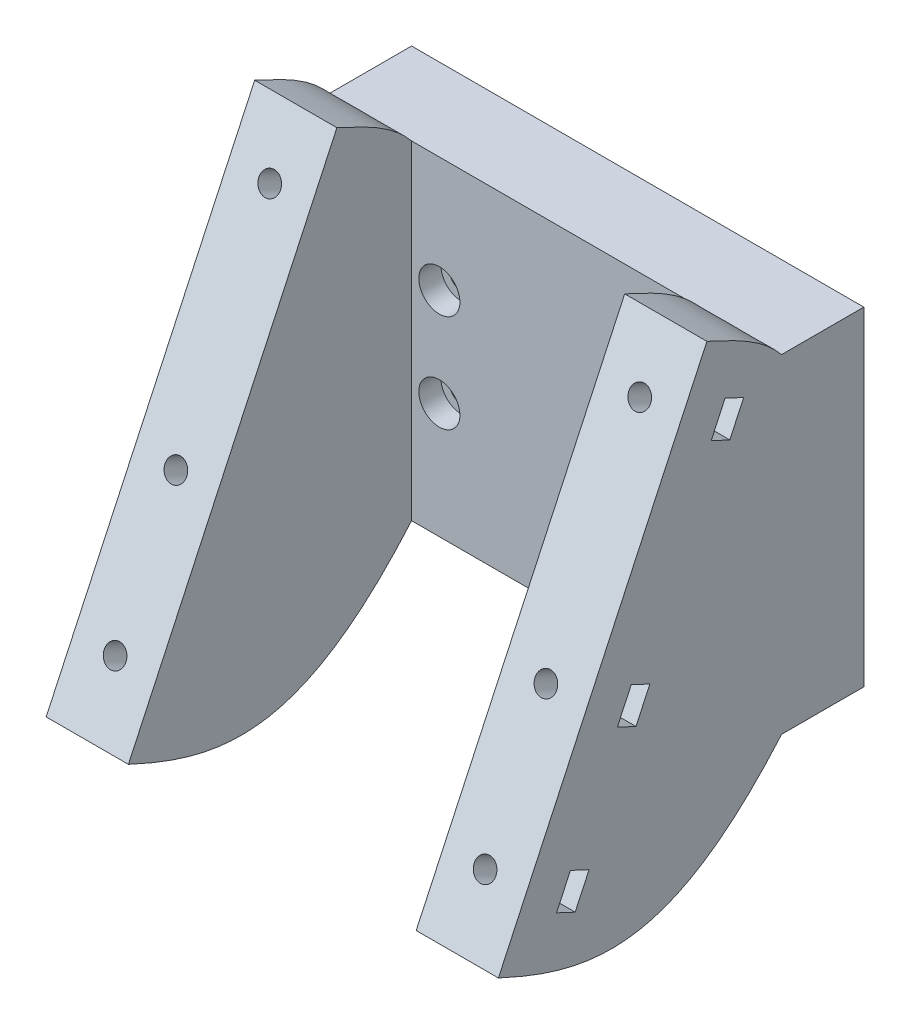
SolidWorks part; units mm, degrees
ref_plane "Płaszczyzna przednia" through (0, 0, 0) normal (0, 0, 1) x (1, 0, 0)
ref_plane "Płaszczyzna górna" through (0, 0, 0) normal (0, 1, 0) x (1, 0, 0)
ref_plane "Płaszczyzna prawa" through (0, 0, 0) normal (1, 0, 0) x (0, 0, -1)
sketch "Szkic1" plane through (0, 0, 0) normal (0, 0, 1) x (1, 0, 0)
  line L0 (-10.5, 0) -> (10.5, 0) construction
  line L1 (-10.5, 32.5) -> (10.5, 32.5) construction
  line L2 (-10.5, -32.5) -> (10.5, -32.5) construction
  line L3 (0, 0) -> (0, 46.2364) construction
  line L5 (55, -40) -> (-55, -40)
  line L6 (55, -40) -> (55, 40)
  line L7 (55, 40) -> (-55, 40)
  line L8 (-55, -40) -> (-55, 40)
  line L9 (55, -40) -> (-55, 40) construction
  line L10 (55, 40) -> (-55, -40) construction
  arc A1 (-10.5, 32.5) -> (-10.5, -32.5) centre (-10.5, 0) ccw construction
  arc A2 (10.5, -32.5) -> (10.5, 32.5) centre (10.5, 0) ccw construction
  point P5 (0, 0)
  point P10 (-28.25, 11.9063)
  point P11 (28.25, 11.9063)
  point P12 (-28.25, -11.9063)
  point P13 (28.25, -11.9063)
  dimension "D5" = 110
  dimension "D2" = 65
  dimension "D3" = 21
  dimension "D4" = 56.5
  dimension "D6" = 80
extrude "Dodanie-wyciągnięcie1" add sketch "Szkic1" along normal blind 20 contours L8 L5 L6 L7
sketch "Szkic4" plane through (0, 0, 20) normal (0, 0, 1) x (1, 0, 0)
  line L0 (0, 0) -> (0, 44.7462) construction
  line L2 (-55, -70) -> (-55, 70)
  line L3 (-55, 70) -> (-35, 70)
  line L4 (-35, -70) -> (-35, 70)
  line L6 (35, -70) -> (35, 70)
  line L7 (35, 70) -> (55, 70)
  line L8 (55, -70) -> (55, 70)
  line L9 (-55, -70) -> (-35, -70)
  line L10 (35, -70) -> (55, -70)
  line L11 (-55, -40) -> (-55, 40) construction
  dimension "D1" = 20
  dimension "D2" = 70
  dimension "D4" = 70
extrude "Dodanie-wyciągnięcie2" add sketch "Szkic4" along normal blind 75
sketch "Szkic7" plane through (0, 0, 0) normal (1, 0, 0) x (0, 0, -1)
  line L1 (-95, -70) -> (-29.7169, 70)
  line L2 (-95, 70) -> (-95, -70)
  line L11 (-29.7169, 70) -> (-95, 70)
  line L14 (-95, -70) -> (-20, -70) construction
  point P0 (0, 0)
  dimension "D1" = 65
extrude "Wytnij-wyciągnięcie2" cut sketch "Szkic7" against normal through all both and the other way through all contours L2 L1 L11
sketch "Szkic11" plane through (0, 0, 20) normal (0, 0, 1) x (1, 0, 0)
  point P0 (28.25, 11.9063)
  point P2 (28.25, -11.9063)
  point P4 (-28.25, -11.9063)
  point P6 (-28.25, 11.9063)
hole_wizard "Pogłębienie walcowe pod M5 Wkręt z łbem walcowym z gniazdem sześciokątnym2" positions "Szkic12" profile "Szkic13" counterbore size "M5" standard "ISO" end condition through all
sketch "Szkic12" plane through (0, 0, 20) normal (0, 0, 1) x (1, 0, 0)
  point P0 (-28.25, 11.9063)
  point P3 (-28.25, -11.9063)
  point P6 (28.25, -11.9063)
  point P9 (28.25, 11.9063)
sketch "Szkic13" plane through (-28.25, 11.9063, 20) normal (1, 0, 0) x (0, -1, 0)
  line L0 (0, 0) -> (0, 20)
  line L1 (0, 20) -> (2.9, 20)
  line L3 (2.9, 20) -> (2.9, 5.4)
  line L4 (2.9, 5.4) -> (5, 5.4)
  line L5 (5, 5.4) -> (5, 0)
  line L7 (5, 0) -> (0, 0)
  line L11 (0, -6.35) -> (0, 107.95) construction
  dimension "Średnica otworu na wylot" = 5.8
  dimension "Głębokość otworu na wylot" = 20
  dimension "Średnica pogłębienia walcowego" = 10
  dimension "Głębokość pogłębienia walcowego" = 5.4
sketch "Szkic14" plane through (-55, 0, 0) normal (-1, 0, 0) x (0, 0, 1)
  line L0 (20, 40) -> (20, 70) construction
  line L1 (116.0727, -44.2045) -> (88.8835, -56.8831) construction
  line L2 (116.0727, -44.2045) -> (88.8835, -56.8831) construction
  line L3 (95, -70) -> (29.7169, 70) construction
  line L4 (95, -70) -> (20, -70) construction
  line L5 (20, -70) -> (20, -40) construction
  line L6 (95, -70) -> (88.8835, -56.8831)
  line L7 (95, -70) -> (20, -70)
  line L8 (20, -70) -> (20, -40)
  line L9 (38.1693, 51.8738) -> (65.3585, 64.5524) construction
  line L10 (38.1693, 51.8738) -> (65.3585, 64.5524) construction
  line L11 (29.7169, 70) -> (20, 70) construction
  line L12 (20, 40) -> (20, 70)
  line L13 (29.7169, 70) -> (20, 70)
  line L14 (95, -70) -> (88.8835, -56.8831)
  line L15 (38.1693, 51.8738) -> (29.7169, 70)
  spline S0 degree 3 poles (88.8835, -56.8831) (65.035, -68.0038) (46.1537, -70.4022) (20, -40) knots 0 0 0 0 1 1 1 1
  spline S1 degree 3 poles (38.1693, 51.8738) (31.4595, 48.745) (24.9204, 45.9385) (20, 40) knots 0 0 0 0 1 1 1 1
  point P12 (0, 0)
  line M3 (95, -70) -> (29.7169, 70)
  line M4 (29.7169, 70) -> (20, 70)
  line M5 (20, 70) -> (20, 40)
  line M9 (20, -40) -> (20, -70)
  line M10 (20, -70) -> (95, -70)
extrude "Wytnij-wyciągnięcie3" cut sketch "Szkic14" against normal through all contours S1 M3 M4 M5 | S0 M3 M9 M10
sketch "Szkic15" plane through (0, 23.8847, 51.2209) normal (0, 0.4226, 0.9063) x (1, 0, 0)
  line L0 (-45, 30.8857) -> (-45, -89.1174) construction
  line L1 (-35, 30.8857) -> (-55, 30.8857) construction
  line L2 (-35, -89.1174) -> (-55, -89.1174) construction
  line L3 (0, 0) -> (0, 55.6313) construction
  line L4 (-35, 30.8826) -> (-55, 30.8826) construction
  point P9 (-45, 15.8857)
  point P10 (-45, -73.1143)
  point P11 (-45, -38.1174)
  point P14 (0, 0)
  dimension "D1" = 15
  dimension "D2" = 69
  dimension "D3" = 104
sketch "Szkic18" plane through (-55, 0, 0) normal (-1, 0, 0) x (0, 0, 1)
  line L0 (44.5073, 38.282) -> (21.5412, 27.5727) construction
  line L1 (67.33, -10.6614) -> (38.9238, -23.9074) construction
  line L2 (82.1203, -42.3794) -> (61.424, -52.0302) construction
  line L3 (38.168, 51.8766) -> (88.8835, -56.8831) construction
  line L4 (51.2209, 23.8847) -> (27.7101, 74.3037) construction
  line L5 (33.7537, 37.681) -> (37.1347, 30.4306)
  line L6 (33.7537, 37.681) -> (29.2222, 35.5679)
  line L7 (37.1347, 30.4306) -> (32.6031, 28.3175)
  line L8 (29.2222, 35.5679) -> (32.6031, 28.3175)
  line L9 (33.7537, 37.681) -> (32.6031, 28.3175) construction
  line L10 (37.1347, 30.4306) -> (29.2222, 35.5679) construction
  line L11 (52.0449, -13.3754) -> (55.4258, -20.6259)
  line L12 (52.0449, -13.3754) -> (56.5764, -11.2623)
  line L13 (55.4258, -20.6259) -> (59.9573, -18.5128)
  line L14 (56.5764, -11.2623) -> (59.9573, -18.5128)
  line L15 (52.0449, -13.3754) -> (59.9573, -18.5128) construction
  line L16 (55.4258, -20.6259) -> (56.5764, -11.2623) construction
  line L17 (66.8352, -45.0935) -> (70.2162, -52.3439)
  line L18 (66.8352, -45.0935) -> (71.3668, -42.9804)
  line L19 (70.2162, -52.3439) -> (74.7477, -50.2308)
  line L20 (71.3668, -42.9804) -> (74.7477, -50.2308)
  line L21 (66.8352, -45.0935) -> (74.7477, -50.2308) construction
  line L22 (70.2162, -52.3439) -> (71.3668, -42.9804) construction
  point P0 (82.1203, -42.3794)
  point P2 (44.5073, 38.282)
  point P4 (67.33, -10.6614)
  point P16 (0, 0)
  point P17 (33.1784, 32.9993)
  point P18 (56.0011, -15.9441)
  point P19 (70.7915, -47.6621)
  point P24 (0, 0)
  point P29 (0, 0)
  dimension "D1" = 15
  dimension "D2" = 8
  dimension "D3" = 5
sketch "Szkic19" plane through (0, 23.8847, 51.2209) normal (0, 0.4226, 0.9063) x (1, 0, 0)
  circle A0 centre (-45, 15.8857) radius 2.65
  circle A1 centre (-45, -73.1143) radius 2.65
  circle A2 centre (-45, -38.1174) radius 2.65
  dimension "D1" = 5.3
extrude "Wytnij-wyciągnięcie4" cut sketch "Szkic19" against normal blind 20
ref_plane "Płaszczyzna1" through (0, 17.5454, 37.6262) normal (0, 0.4226, 0.9063) x (1, 0, 0)
sketch "Szkic20" plane through (0, 17.5454, 37.6262) normal (0, 0.4226, 0.9063) x (1, 0, 0)
  line L0 (-45, 30.8857) -> (-45, -89.1174) construction
  line L1 (-42.6906, 19.8857) -> (-47.3094, 19.8857)
  line L2 (-47.3094, 19.8857) -> (-49.6188, 15.8857)
  line L3 (-49.6188, 15.8857) -> (-47.3094, 11.8857)
  line L4 (-47.3094, 11.8857) -> (-42.6906, 11.8857)
  line L5 (-42.6906, 11.8857) -> (-40.3812, 15.8857)
  line L6 (-40.3812, 15.8857) -> (-42.6906, 19.8857)
  line L8 (-42.6906, -34.1174) -> (-47.3094, -34.1174)
  line L9 (-47.3094, -34.1174) -> (-49.6188, -38.1174)
  line L10 (-49.6188, -38.1174) -> (-47.3094, -42.1174)
  line L11 (-47.3094, -42.1174) -> (-42.6906, -42.1174)
  line L12 (-42.6906, -42.1174) -> (-40.3812, -38.1174)
  line L13 (-40.3812, -38.1174) -> (-42.6906, -34.1174)
  line L14 (-42.6906, -69.1143) -> (-47.3094, -69.1143)
  line L15 (-47.3094, -69.1143) -> (-49.6188, -73.1143)
  line L16 (-49.6188, -73.1143) -> (-47.3094, -77.1143)
  line L17 (-47.3094, -77.1143) -> (-42.6906, -77.1143)
  line L18 (-42.6906, -77.1143) -> (-40.3812, -73.1143)
  line L19 (-40.3812, -73.1143) -> (-42.6906, -69.1143)
  circle A0 centre (-45, 15.8857) radius 4 construction
  circle A1 centre (-45, -38.1174) radius 4 construction
  circle A2 centre (-45, -73.1143) radius 4 construction
  dimension "D1" = 8
extrude "Wytnij-wyciągnięcie5" cut sketch "Szkic20" along normal blind 5
ref_plane "Płaszczyzna2" through (-45, 0, 0) normal (-1, 0, 0) x (0, 0, 1)
extrude "Wytnij-wyciągnięcie6" cut sketch "Szkic18" against normal up to surface (10 mm away) up to plane "Płaszczyzna2"
mirror "Lustro2" about plane through (0, 0, 0) normal (1, 0, 0) of "Wytnij-wyciągnięcie4", "Wytnij-wyciągnięcie5", "Wytnij-wyciągnięcie6"
